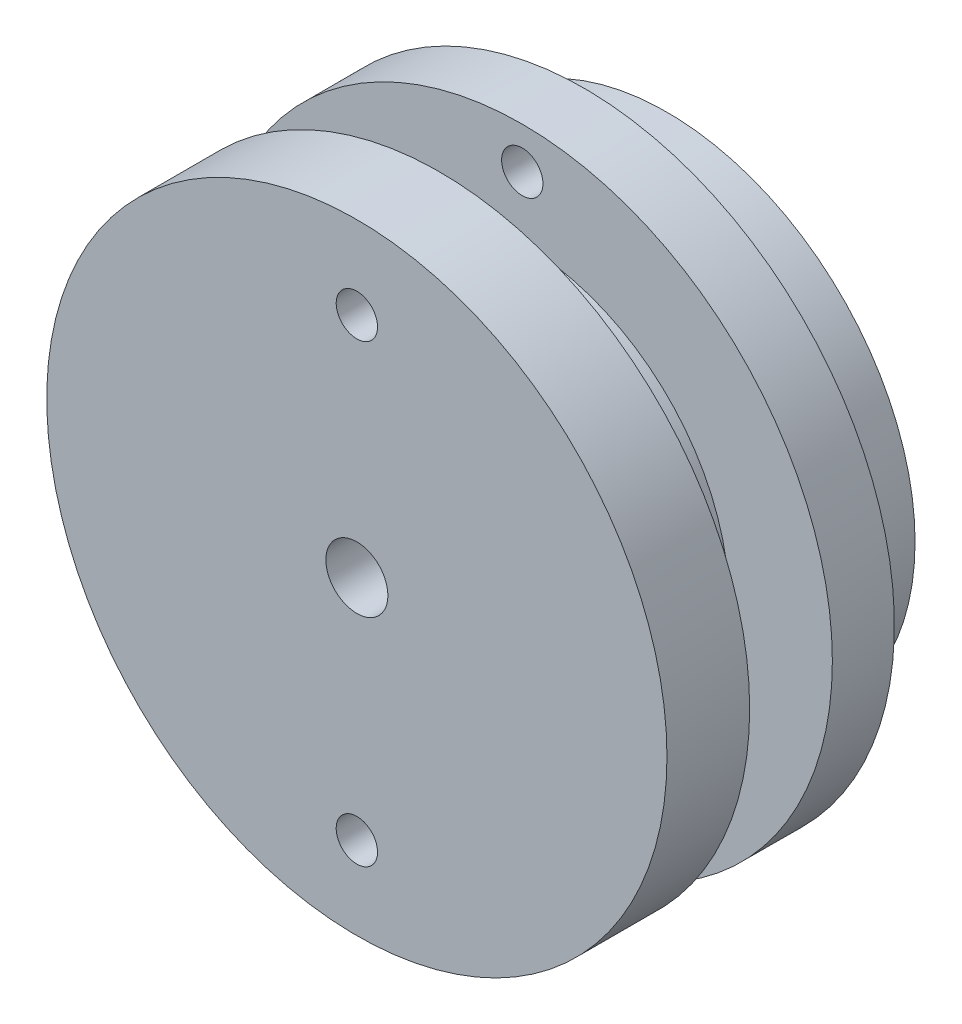
SolidWorks part; units mm, degrees
ref_plane "Front Plane" through (0, 0, 0) normal (0, 0, 1) x (1, 0, 0)
ref_plane "Top Plane" through (0, 0, 0) normal (0, 1, 0) x (1, 0, 0)
ref_plane "Right Plane" through (0, 0, 0) normal (1, 0, 0) x (0, 0, -1)
sketch "Sketch1" plane through (0, 0, 0) normal (0, 0, 1) x (1, 0, 0)
  line L0 (-4.65, -4.65) -> (-4.65, 4.65)
  line L1 (0, 0) -> (-7.75, 0) construction
  line L2 (-4.65, 4.65) -> (4.65, 4.65)
  line L3 (4.65, 4.65) -> (4.65, -4.65)
  line L4 (4.65, -4.65) -> (-4.65, -4.65)
  line L5 (0, 0) -> (7.75, 0) construction
  line L6 (0, 0) -> (0, 7.75) construction
  line L7 (0, 0) -> (0, -7.75) construction
  arc A0 (-7.9111, -1.1891) -> (-1.1891, -7.9111) centre (0, 0) ccw construction
  circle A1 centre (0, 0) radius 15
  arc A2 (1.1891, -7.9111) -> (7.9111, -1.1891) centre (0, 0) ccw construction
  arc A3 (7.9111, 1.1891) -> (1.1891, 7.9111) centre (0, 0) ccw construction
  circle A4 centre (0, 7.75) radius 1.2
  circle A5 centre (7.75, 0) radius 1.2
  circle A6 centre (0, -7.75) radius 1.2
  circle A7 centre (-7.75, 0) radius 1.2
  arc A8 (-1.1891, 7.9111) -> (-7.9111, 1.1891) centre (0, 0) ccw construction
extrude "Boss-Extrude1" add sketch "Sketch1" along normal blind 7
sketch "Sketch2" plane through (0, 0, 7) normal (0, 0, 1) x (1, 0, 0)
  line L0 (-4.65, 4.65) -> (-3.3, 4.65)
  line L1 (4.65, 4.65) -> (-4.65, 4.65) construction
  line L2 (-3.3, 4.65) -> (-3.3, -4.65)
  line L3 (-4.65, -4.65) -> (4.65, -4.65) construction
  line L4 (-3.3, -4.65) -> (-4.65, -4.65)
  line L5 (-4.65, 4.65) -> (-4.65, -4.65) construction
  line L6 (-4.65, -4.65) -> (-4.65, 4.65)
  line L8 (4.65, -4.65) -> (4.65, 4.65)
  line L9 (3.3, -4.65) -> (4.65, -4.65)
  line L10 (3.3, 4.65) -> (3.3, -4.65)
  line L11 (4.65, 4.65) -> (3.3, 4.65)
  circle A0 centre (0, 0) radius 10
  circle A1 centre (0, 0) radius 1.5
extrude "Boss-Extrude2" add sketch "Sketch2" along normal blind 4
sketch "Sketch3" plane through (0, 0, 11) normal (0, 0, 1) x (1, 0, 0)
  circle A0 centre (0, 0) radius 1.5
  circle A1 centre (0, 0) radius 15
extrude "Boss-Extrude3" add sketch "Sketch3" along normal blind 4
sketch "Sketch4" plane through (0, 0, 0) normal (0, 0, -1) x (-1, 0, 0)
  circle A0 centre (0, 0) radius 12
  circle A1 centre (0, 0) radius 15
extrude "Cut-Extrude1" cut sketch "Sketch4" against normal blind 4
sketch "Sketch5" plane through (0, 0, 4) normal (0, 0, -1) x (-1, 0, 0)
  line L1 (0, 0) -> (15, 0) construction
  circle A1 centre (0, 13) radius 1
  circle A2 centre (0, 0) radius 15 construction
  circle A3 centre (0, -13) radius 1
extrude "Cut-Extrude2" cut sketch "Sketch5" against normal up to surface (3 mm away) up to face at (10, 0, 7)
sketch "Sketch6" plane through (0, 0, 11) normal (0, 0, -1) x (-1, 0, 0)
  line L0 (0, 0) -> (0, 10) construction
  line L1 (0, 10) -> (0, 11) construction
  line L2 (0, 0) -> (10, 0) construction
  circle A0 centre (0, 0) radius 10 construction
  circle A1 centre (0, 11) radius 1
  circle A2 centre (0, -11) radius 1
extrude "Cut-Extrude5" cut sketch "Sketch6" against normal through all
